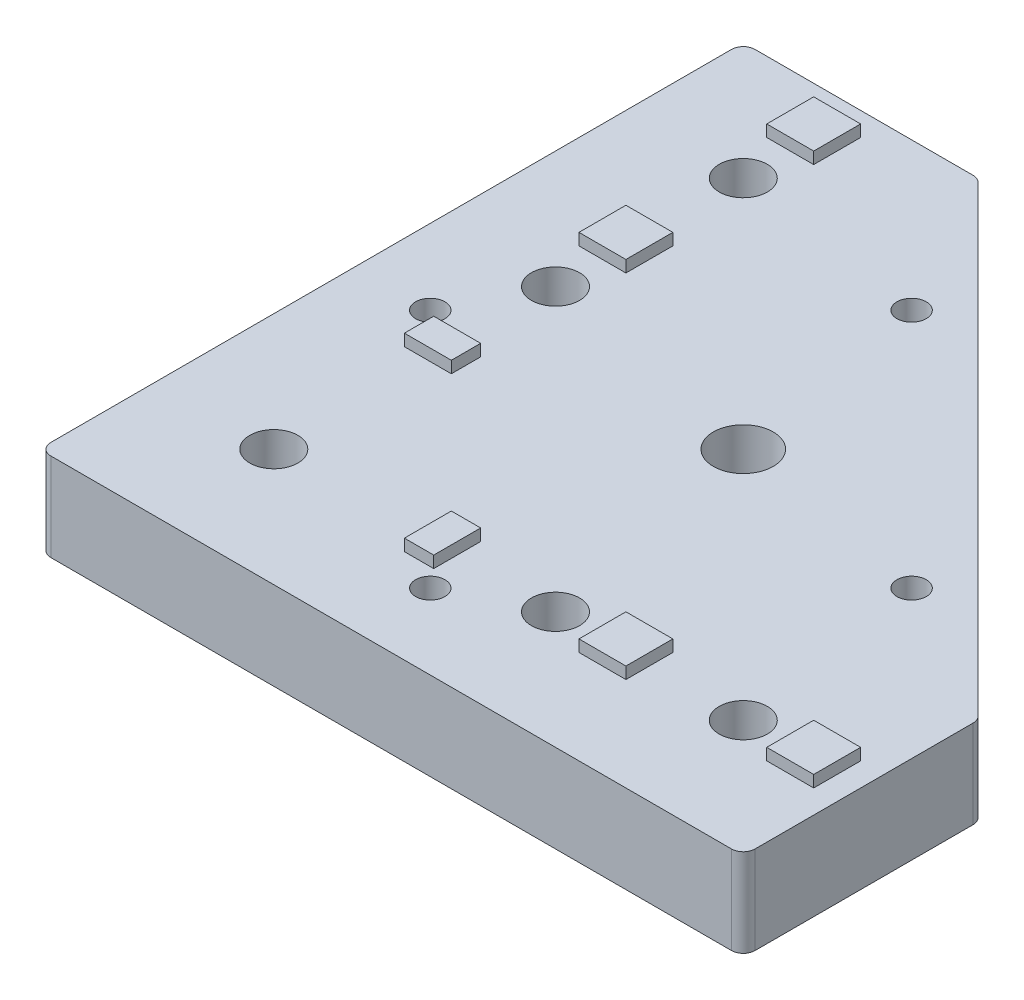
SolidWorks part; units mm, degrees
material "Алюминиевый сплав"
ref_plane "Спереди" through (0, 0, 0) normal (0, 0, 1) x (1, 0, 0)
ref_plane "Сверху" through (0, 0, 0) normal (0, 1, 0) x (1, 0, 0)
ref_plane "Справа" through (0, 0, 0) normal (1, 0, 0) x (0, 0, -1)
sketch "Эскиз1" plane through (0, 0, 0) normal (0, 1, 0) x (1, 0, 0)
  line L0 (0, 0) -> (0, 120)
  line L1 (0, 120) -> (40, 120)
  line L2 (40, 120) -> (120, 40)
  line L3 (120, 40) -> (120, 0)
  line L4 (120, 0) -> (0, 0)
  point P3 (1.2064, 0)
  dimension "D1" = 120
  dimension "D2" = 40
extrude "Бобышка-Вытянуть1" add sketch "Эскиз1" along normal blind 15
hole_wizard "Отверстие обработанное метчиком M121" positions "Эскиз2" profile "Эскиз3" tap size "M12" standard "ISO" end condition up to next
sketch "Эскиз2" plane through (0, 15, 0) normal (0, 1, 0) x (1, 0, 0)
  line L0 (0, 0) -> (120, 0) construction
  line L2 (120, 0) -> (120, 40) construction
  point P0 (60, 60)
  dimension "D1" = 60
  dimension "D2" = 60
sketch "Эскиз3" plane through (60, 15, -60) normal (1, 0, 0) x (0, 0, 1)
  line L0 (0, 0) -> (0, 15)
  line L1 (0, 15) -> (5.1, 15)
  line L2 (5.1, 15) -> (5.1, 0)
  line L5 (5.1, 0) -> (0, 0)
  line L11 (0, -6.35) -> (0, 107.95) construction
  dimension "Диаметр проходного сверла" = 10.2
  dimension "Глубина проходного сверла" = 15
cosmetic thread "Отверстие резьбы1" parameters "D2"=12
hole_wizard "Отверстие обработанное метчиком M62" positions "Эскиз4" profile "Эскиз5" tap size "M6" standard "ISO" end condition up to next
sketch "Эскиз4" plane through (0, 15, 0) normal (0, 1, 0) x (1, 0, 0)
  line L0 (53.837, 94.8492) -> (12.8249, 53.837)
  line L1 (12.8249, 53.837) -> (53.837, 12.8249)
  line L2 (53.837, 12.8249) -> (94.8492, 53.837)
  line L3 (94.8492, 53.837) -> (53.837, 94.8492)
  line L5 (120, 40) -> (40, 120) construction
  line L8 (53.837, 94.8492) -> (53.837, 12.8249)
  line L9 (33.331, 33.331) -> (0, 0)
  point P0 (53.837, 94.8492)
  point P2 (94.8492, 53.837)
  point P4 (53.837, 12.8249)
  point P6 (12.8249, 53.837)
  point P48 (52.467, 11.4548)
  dimension "D1" = 58
  dimension "D2" = 58
  dimension "D3" = 8
sketch "Эскиз5" plane through (53.837, 15, -94.8492) normal (1, 0, 0) x (0, 0, 1)
  line L0 (0, 0) -> (0, 15)
  line L1 (0, 15) -> (2.5, 15)
  line L2 (2.5, 15) -> (2.5, 0)
  line L5 (2.5, 0) -> (0, 0)
  line L11 (0, -6.35) -> (0, 107.95) construction
  dimension "Диаметр проходного сверла" = 5
  dimension "Глубина проходного сверла" = 15
cosmetic thread "Отверстие резьбы2" parameters "D2"=6
cosmetic thread "Отверстие резьбы3" parameters "D2"=6
cosmetic thread "Отверстие резьбы4" parameters "D2"=6
cosmetic thread "Отверстие резьбы5" parameters "D2"=6
hole_wizard "Диаметр отверстия Ø8.2 (8.2)1" positions "Эскиз6" profile "Эскиз8" hole size "Ø8.2" standard "ISO" end condition up to next
sketch "Эскиз6" plane through (0, 15, 0) normal (0, 1, 0) x (1, 0, 0)
  line L0 (100, 20) -> (68, 20)
  line L1 (68, 20) -> (20, 20)
  line L2 (20, 20) -> (20, 68)
  line L3 (20, 68) -> (20, 100)
  line L5 (0, 0) -> (120, 0) construction
  line L6 (0, 120) -> (0, 0) construction
  point P0 (20, 100)
  point P2 (20, 68)
  point P4 (20, 20)
  point P6 (68, 20)
  point P8 (100, 20)
  dimension "D1" = 20
  dimension "D2" = 20
  dimension "D3" = 48
  dimension "D4" = 32
sketch "Эскиз8" plane through (20, 15, -100) normal (1, 0, 0) x (0, 0, 1)
  line L0 (0, 0) -> (0, 15)
  line L1 (0, 15) -> (4.1, 15)
  line L2 (4.1, 15) -> (4.1, 0)
  line L5 (4.1, 0) -> (0, 0)
  line L11 (0, -6.35) -> (0, 107.95) construction
  dimension "Диаметр сквозного отверстия" = 8.2
  dimension "Глубина сквозного отверстия" = 15
sketch "Эскиз9" plane through (0, 15, 0) normal (0, 1, 0) x (1, 0, 0)
  line L0 (0, 0) -> (80, 80) construction
  line L1 (16, 116) -> (24, 116)
  line L2 (16, 116) -> (16, 108)
  line L3 (16, 108) -> (24, 108)
  line L4 (24, 116) -> (24, 108)
  line L5 (16, 116) -> (24, 108) construction
  line L6 (16, 108) -> (24, 116) construction
  line L7 (16, 84) -> (24, 84)
  line L8 (16, 84) -> (16, 76)
  line L9 (16, 76) -> (24, 76)
  line L10 (24, 84) -> (24, 76)
  line L11 (16, 84) -> (24, 76) construction
  line L12 (16, 76) -> (24, 84) construction
  line L13 (16, 51.25) -> (24, 51.25)
  line L14 (16, 51.25) -> (16, 46.25)
  line L15 (16, 46.25) -> (24, 46.25)
  line L16 (24, 51.25) -> (24, 46.25)
  line L17 (16, 51.25) -> (24, 46.25) construction
  line L18 (16, 46.25) -> (24, 51.25) construction
  line L19 (120, 40) -> (40, 120) construction
  line L20 (20, 112) -> (20, 100) construction
  line L21 (20, 100) -> (20, 80) construction
  line L22 (20, 80) -> (20, 48.75) construction
  line L23 (80, 20) -> (48.75, 20) construction
  line L24 (100, 20) -> (80, 20) construction
  line L25 (112, 20) -> (100, 20) construction
  line L26 (46.25, 16) -> (51.25, 24) construction
  line L27 (51.25, 16) -> (46.25, 24) construction
  line L28 (76, 16) -> (84, 24) construction
  line L29 (84, 16) -> (76, 24) construction
  line L30 (108, 16) -> (116, 24) construction
  line L31 (116, 16) -> (108, 24) construction
  line L32 (51.25, 24) -> (46.25, 24)
  line L33 (46.25, 16) -> (46.25, 24)
  line L34 (51.25, 16) -> (46.25, 16)
  line L35 (51.25, 16) -> (51.25, 24)
  line L36 (84, 24) -> (76, 24)
  line L37 (76, 16) -> (76, 24)
  line L38 (84, 16) -> (76, 16)
  line L39 (84, 16) -> (84, 24)
  line L40 (116, 24) -> (108, 24)
  line L41 (108, 16) -> (108, 24)
  line L42 (116, 16) -> (108, 16)
  line L43 (116, 16) -> (116, 24)
  line L44 (40, 120) -> (0, 120) construction
  point P0 (20, 112)
  point P5 (20, 80)
  point P10 (20, 48.75)
  point P23 (12, 80.1439)
  point P26 (12, 65.5613)
  point P31 (18, 33.6701)
  point P32 (18, 30.3688)
  point P51 (48.75, 20)
  point P52 (80, 20)
  point P53 (112, 20)
  dimension "D5" = 24.75
  dimension "D1" = 8
  dimension "D2" = 24
  dimension "D3" = 4
  dimension "D4" = 5
extrude "Бобышка-Вытянуть2" add sketch "Эскиз9" along normal blind 2
fillet "Скругление1" radius 2 5 edges at (0, 7.5, -120) (0, 7.5, 0) (120, 7.5, 0) (120, 7.5, -40) (40, 7.5, -120)
